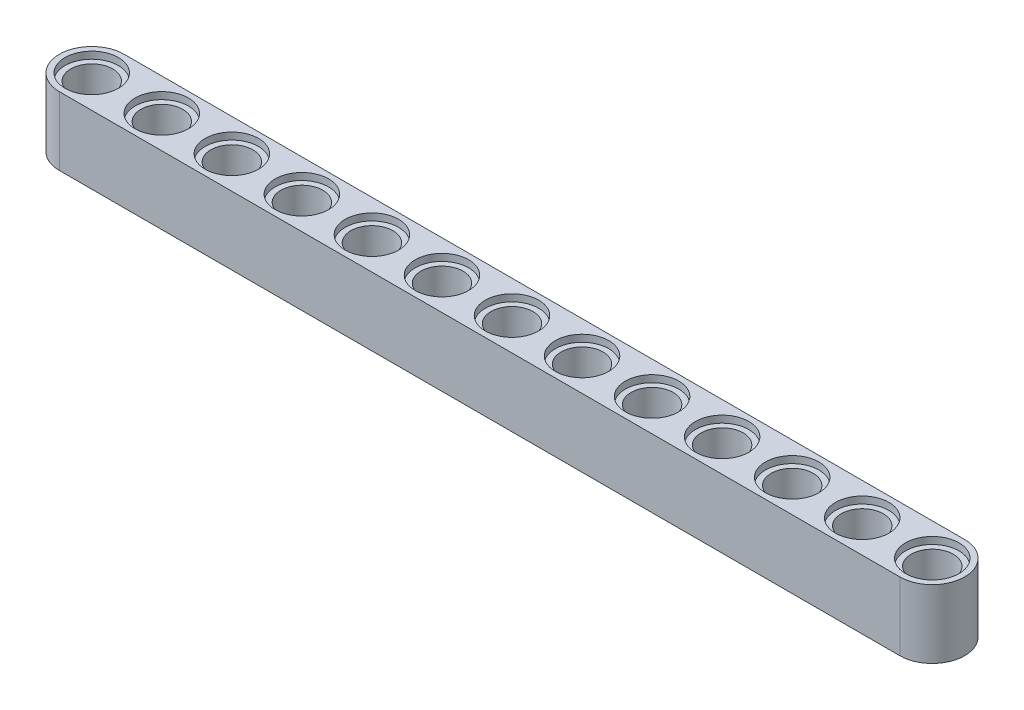
SolidWorks part; units mm, degrees
ref_plane "Front Plane" through (0, 0, 0) normal (0, 0, 1) x (1, 0, 0)
ref_plane "Top Plane" through (0, 0, 0) normal (0, 1, 0) x (1, 0, 0)
ref_plane "Right Plane" through (0, 0, 0) normal (1, 0, 0) x (0, 0, -1)
sketch "Sketch1" plane through (0, 0, 0) normal (0, 1, 0) x (1, 0, 0)
  line L0 (-16, -3.7) -> (80, -3.7)
  line L1 (-16, 3.7) -> (80, 3.7)
  arc A9 (80, 3.7) -> (80, -3.7) centre (80, 0) cw
  arc A10 (-16, 3.7) -> (-16, -3.7) centre (-16, 0) ccw
  point P20 (8, -3.7)
  point P25 (-8, -3.7)
  dimension "D1" = 3.7
  dimension "D5" = 3.7
  dimension "D2" = 96
extrude "Boss-Extrude3" add sketch "Sketch1" along normal blind 7.8 contours A10 L0 A9 L1
sketch "Sketch2" plane through (0, 7.8, 0) normal (0, 1, 0) x (1, 0, 0)
  circle A0 centre (0, 0) radius 2.4
  circle A2 centre (8, 0) radius 2.4
  circle A5 centre (16, 0) radius 2.4
  circle A6 centre (-16, 0) radius 2.4
  circle A9 centre (-8, 0) radius 2.4
  circle A10 centre (24, 0) radius 2.4
  circle A11 centre (32, 0) radius 2.4
  circle A12 centre (40, 0) radius 2.4
  circle A13 centre (48, 0) radius 2.4
  circle A14 centre (56, 0) radius 2.4
  circle A15 centre (64, 0) radius 2.4
  circle A16 centre (72, 0) radius 2.4
  circle A17 centre (80, 0) radius 2.4
  dimension "D1" = 4.8
  dimension "D2" = 8
sketch "Sketch3" plane through (0, 7.8, 0) normal (0, 1, 0) x (1, 0, 0)
  circle A0 centre (0, 0) radius 3.05
  circle A1 centre (8, 0) radius 3.05
  circle A2 centre (16, 0) radius 3.05
  circle A3 centre (-16, 0) radius 3.05
  circle A4 centre (-8, 0) radius 3.05
  circle A5 centre (32, 0) radius 3.05
  circle A6 centre (24, 0) radius 3.05
  circle A7 centre (40, 0) radius 3.05
  circle A8 centre (48, 0) radius 3.05
  circle A9 centre (56, 0) radius 3.05
  circle A10 centre (64, 0) radius 3.05
  circle A11 centre (72, 0) radius 3.05
  circle A12 centre (80, 0) radius 3.05
  dimension "D1" = 6.1
  dimension "D2" = 8
sketch "Sketch4" plane through (0, 0, 0) normal (0, -1, 0) x (1, 0, 0)
  circle A0 centre (0, 0) radius 3.05
  circle A1 centre (8, 0) radius 3.05
  circle A2 centre (16, 0) radius 3.05
  circle A3 centre (-16, 0) radius 3.05
  circle A4 centre (-8, 0) radius 3.05
  circle A5 centre (32, 0) radius 3.05
  circle A6 centre (24, 0) radius 3.05
  circle A7 centre (40, 0) radius 3.05
  circle A8 centre (48, 0) radius 3.05
  circle A9 centre (56, 0) radius 3.05
  circle A10 centre (64, 0) radius 3.05
  circle A11 centre (72, 0) radius 3.05
  circle A12 centre (80, 0) radius 3.05
  dimension "D1" = 6.1
  dimension "D2" = 8
extrude "Cut-Extrude4" cut sketch "Sketch2" against normal blind 7.8
extrude "Cut-Extrude5" cut sketch "Sketch3" against normal blind 0.8
extrude "Cut-Extrude6" cut sketch "Sketch4" against normal blind 0.8
